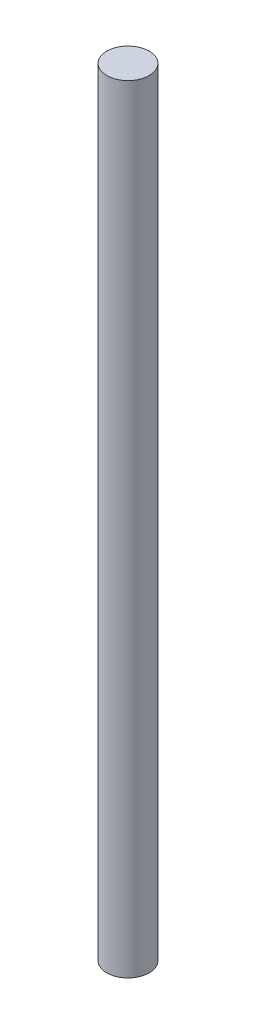
SolidWorks part; units mm, degrees
ref_plane "Front" through (0, 0, 0) normal (0, 0, 1) x (1, 0, 0)
ref_plane "Top" through (0, 0, 0) normal (0, 1, 0) x (1, 0, 0)
ref_plane "Right" through (0, 0, 0) normal (1, 0, 0) x (0, 0, -1)
sketch "Sketch1" plane through (0, 0, 0) normal (0, 1, 0) x (1, 0, 0)
  circle A0 centre (0, 0) radius 1.5
  dimension "D1" = 3
extrude "Boss-Extrude1" add sketch "Sketch1" along normal blind 55
